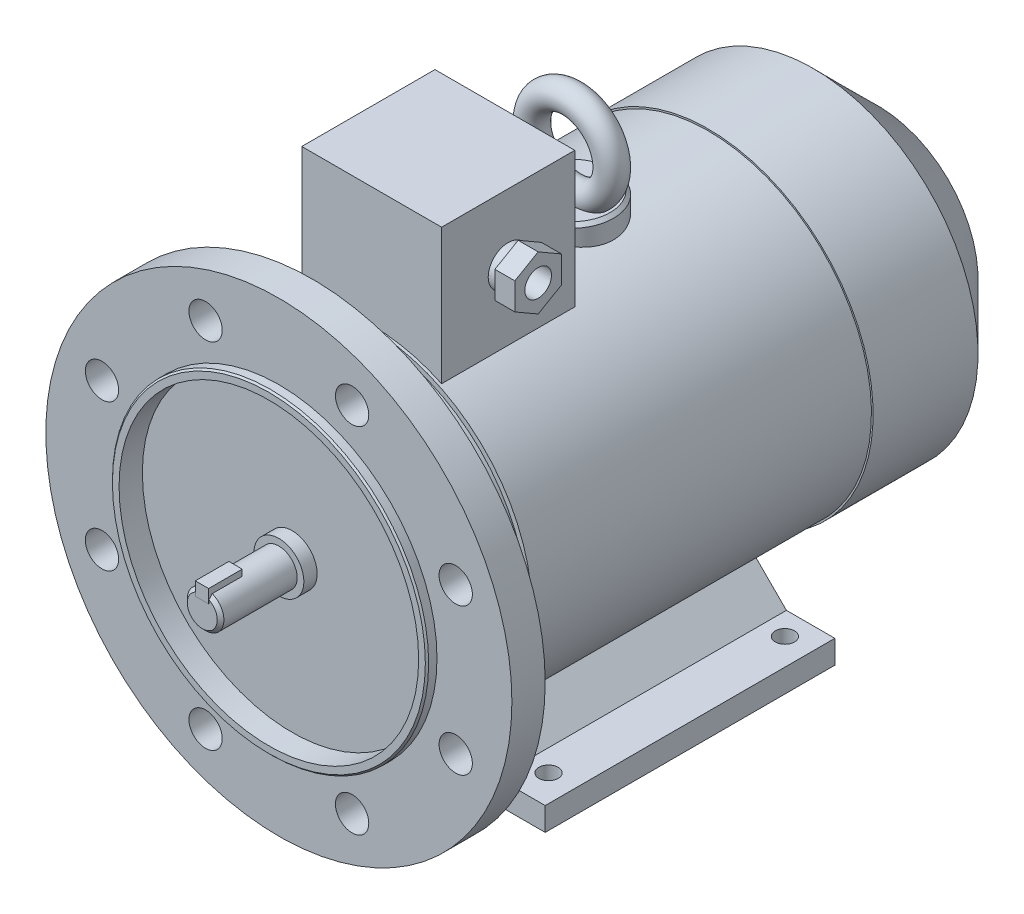
SolidWorks part; units mm, degrees
material "Ст.3 ГОСТ 380-88"
ref_plane "Спереди" through (0, 0, 0) normal (0, 0, 1) x (1, 0, 0)
ref_plane "Сверху" through (0, 0, 0) normal (0, 1, 0) x (1, 0, 0)
ref_plane "Справа" through (0, 0, 0) normal (1, 0, 0) x (0, 0, -1)
sketch "Эскиз1" plane through (0, 0, 0) normal (0, 0, 1) x (1, 0, 0)
  circle A0 centre (0, 0) radius 5.5
  dimension "D1" = 11
extrude "Вытянуть1" add sketch "Эскиз1" along normal blind 23
sketch "Эскиз2" plane through (0, 0, 23) normal (0, 0, 1) x (1, 0, 0)
  line L0 (0, 0) -> (0, 7.7807) construction
  line L1 (-2, 7) -> (2, 7)
  line L2 (-2, 7) -> (-2, 3)
  line L3 (-2, 3) -> (2, 3)
  line L4 (2, 7) -> (2, 3)
  circle A3 centre (0, 0) radius 5.5 construction
  dimension "D1" = 4
  dimension "D2" = 4
  dimension "D3" = 1.5
extrude "Вытянуть2" add sketch "Эскиз2" against normal blind 10 and the other way blind 0.1
sketch "Эскиз3" plane through (0, 0, 0) normal (0, 0, -1) x (-1, 0, 0)
  circle A0 centre (0, 0) radius 7.5
  dimension "D1" = 15
extrude "Вытянуть11" add sketch "Эскиз3" along normal blind 4
sketch "Эскиз16" plane through (0, 0, 0) normal (0, 0, 1) x (1, 0, 0)
  circle A0 centre (0, 0) radius 47.5
  circle A1 centre (0, 0) radius 70
  dimension "D1" = 95
  dimension "D2" = 140
extrude "Вытянуть13" add sketch "Эскиз16" against normal blind 10
sketch "Эскиз17" plane through (0, 0, -4) normal (0, 0, -1) x (-1, 0, 0)
  circle A0 centre (0, 0) radius 47.5
  dimension "D1" = 95
extrude "Вытянуть14" add sketch "Эскиз17" along normal blind 23
sketch "Эскиз18" plane through (0, 0, 0) normal (0, 0, 1) x (1, 0, 0)
  line L0 (0, 0) -> (0, 77.9559) construction
  line L1 (0, 0) -> (-29.3555, 70.8705) construction
  circle A0 centre (-22.0043, 53.1231) radius 5
  circle A3 centre (22.0043, 53.1231) radius 5
  circle A4 centre (53.1231, 22.0043) radius 5
  circle A5 centre (53.1231, -22.0043) radius 5
  circle A6 centre (22.0043, -53.1231) radius 5
  circle A7 centre (-22.0043, -53.1231) radius 5
  circle A8 centre (-53.1231, -22.0043) radius 5
  circle A9 centre (-53.1231, 22.0043) radius 5
  dimension "D2" = 10
  dimension "D1" = 22.5
  dimension "D3" = 57.5
  dimension "D4" = 57.5
  dimension "D5" = 57.5
extrude "Вырез-Вытянуть4" cut sketch "Эскиз18" against normal through all
sketch "Эскиз20" plane through (0, 0, -27) normal (0, 0, -1) x (-1, 0, 0)
  circle A0 centre (0, 0) radius 49
  dimension "D1" = 98
extrude "Вытянуть15" add sketch "Эскиз20" along normal blind 102
sketch "Эскиз21" plane through (0, 0, -129) normal (0, 0, -1) x (-1, 0, 0)
  circle A0 centre (0, 0) radius 49.5
  dimension "D1" = 99
extrude "Вытянуть16" add sketch "Эскиз21" along normal blind 51
chamfer "Фаска3" distance 19.5 angle 45 1 edges at (-49.5, 0, -180)
sketch "Эскиз22" plane through (0, 0, -27) normal (0, 0, 1) x (1, 0, 0)
  line L0 (-53, -56) -> (-32.6463, -56)
  line L1 (-32.6463, -56) -> (-14.1724, -37.5262)
  line L2 (-53, -56) -> (-53, -49)
  line L3 (-42, -56) -> (-44.9041, -56)
  line L4 (-53, -49) -> (-35.5458, -49)
  line L5 (-19.297, -32.7512) -> (-14.1724, -37.5262)
  line L6 (33.8559, -56) -> (53, -56)
  line L7 (-35.5458, -49) -> (-19.297, -32.7512)
  line L8 (42, -56) -> (43.6391, -56)
  line L9 (53, -56) -> (53, -49)
  line L10 (53, -49) -> (38.4542, -49)
  line L11 (33.8559, -56) -> (15.2435, -37.3877)
  line L12 (0, 0) -> (0, -80.1176) construction
  line L13 (38.4542, -49) -> (25.0733, -35.619)
  line L14 (25.0733, -35.619) -> (15.2435, -37.3877)
  circle A0 centre (0, 0) radius 70 construction
  circle M1 centre (0, 0) radius 49
  circle M2 centre (0, 0) radius 47.5
  dimension "D1" = 56
  dimension "D2" = 45
  dimension "D3" = 45
  dimension "D4" = 7
  dimension "D5" = 8.2013
  dimension "D6" = 7
  dimension "D7" = 7
  dimension "D8" = 106
  dimension "D9" = 53
  dimension "D10" = 74
  dimension "D11" = 66.5022
  dimension "D12" = 32.7512
  dimension "D13" = 35.619
  dimension "D14" = 37.5262
  dimension "D15" = 37.3877
extrude "Вытянуть17" add sketch "Эскиз22" against normal blind 87 contours L7 L4 L2 L0 L1 M1 | L7 L1 M1 M2 | L7 L1 L5 M2 | L10 L13 L11 L6 L9 M1 | L13 L14 L11 M2
sketch "Эскиз23" plane through (0, -56, 0) normal (0, -1, 0) x (1, 0, 0)
  line L0 (77.3931, -36) -> (-61.3551, -36) construction
  line L1 (77.3931, -107) -> (-64.6709, -107) construction
  line L2 (5.5, 23) -> (-5.5, 23) construction
  line L4 (45, -36) -> (-45, -36) construction
  line L5 (45, -36) -> (45, -107) construction
  circle A0 centre (45, -36) radius 2.9
  circle A1 centre (-45, -36) radius 2.9
  circle A2 centre (45, -107) radius 2.9
  circle A3 centre (-45, -107) radius 2.9
  dimension "D3" = 5.8
  dimension "D6" = 71
  dimension "D7" = 90
  dimension "D8" = 5.8
  dimension "D9" = 5.8
  dimension "D1" = 59
  dimension "D2" = 71
  dimension "D4" = 45
  dimension "D5" = 90
  dimension "D10" = 59
extrude "Вырез-Вытянуть5" cut sketch "Эскиз23" against normal up to next
ref_plane "Плоскость1" through (0, 42, 0) normal (0, 1, 0) x (-1, 0, 0)
sketch "Эскиз24" plane through (0, 42, 0) normal (0, 1, 0) x (-1, 0, 0)
  line L0 (0, 0) -> (0, -195.5205) construction
  line L1 (-21, -27.8856) -> (21, -27.8856)
  line L2 (-21, -27.8856) -> (-21, -67.8856)
  line L3 (-21, -67.8856) -> (21, -67.8856)
  line L4 (21, -27.8856) -> (21, -67.8856)
  line L7 (49, -27) -> (-49, -27) construction
  dimension "D1" = 42
  dimension "D2" = 42
  dimension "D3" = 40
  dimension "D4" = 40.8856
extrude "Вытянуть18" add sketch "Эскиз24" along normal blind 43
sketch "Эскиз25" plane through (0, 42, 0) normal (0, 1, 0) x (-1, 0, 0)
  line L0 (0, 0) -> (0, -180) construction
  line L1 (-30, -180) -> (30, -180) construction
  circle A0 centre (0, -88) radius 12.5
  dimension "D1" = 25
  dimension "D2" = 88
extrude "Вытянуть19" add sketch "Эскиз25" along normal blind 12
chamfer "Фаска4" distance 1 angle 45 1 edges at (0, 54, -75.5)
ref_plane "Плоскость2" through (0, 0, -88) normal (0, 0, 1) x (1, 0, 0)
sketch "Эскиз26" plane through (0, 0, -88) normal (0, 0, 1) x (1, 0, 0)
  line L0 (11.5, 54) -> (-11.5, 54) construction
  line L1 (0, 0) -> (0, 106.2294) construction
  circle A0 centre (0, 66) radius 12
  dimension "D1" = 24
sketch "Эскиз27" plane through (0, 0, 0) normal (1, 0, 0) x (0, 0, -1)
  line L0 (88, 0) -> (88, 106.2294) construction
  line L1 (99.5, 54) -> (76.5, 54) construction
  line L2 (88, 77) -> (88, -77) construction
  circle A0 centre (88, 78) radius 4
  dimension "D1" = 24
  dimension "D2" = 8
sweep "По траектории1" add profiles "Эскиз27" path "Эскиз26"
chamfer "Фаска5" distance 1 angle 45 1 edges at (0, -5.5, 23)
sketch "Эскиз28" plane through (0, 0, -4) normal (0, 0, 1) x (1, 0, 0)
  circle A0 centre (0, 0) radius 47.5
  circle A1 centre (0, 0) radius 45
  dimension "D1" = 90
  dimension "D2" = 95
extrude "Вытянуть20" add sketch "Эскиз28" along normal blind 7
chamfer "Фаска6" distance 0.5 angle 45 1 edges at (47.5, 0, 3)
sketch "Эскиз29" plane through (21, 0, 0) normal (1, 0, 0) x (0, 0, -1)
  line L0 (27.8856, 85) -> (67.8856, 85) construction
  line L1 (27.8856, 85) -> (27.8856, 44.2719) construction
  circle A0 centre (47.8856, 65) radius 6
  dimension "D3" = 12
  dimension "D1" = 20
  dimension "D2" = 20
extrude "Вытянуть21" add sketch "Эскиз29" along normal blind 3
sketch "Эскиз30" plane through (24, 0, 0) normal (1, 0, 0) x (0, 0, -1)
  line L0 (47.8856, 65) -> (47.8856, 88.5651) construction
  line L1 (47.8856, 73.0829) -> (40.8856, 69.0415)
  line L2 (40.8856, 69.0415) -> (40.8856, 60.9585)
  line L3 (40.8856, 60.9585) -> (47.8856, 56.9171)
  line L4 (47.8856, 56.9171) -> (54.8856, 60.9585)
  line L5 (54.8856, 60.9585) -> (54.8856, 69.0415)
  line L6 (54.8856, 69.0415) -> (47.8856, 73.0829)
  circle A0 centre (47.8856, 65) radius 7 construction
  circle A1 centre (47.8856, 65) radius 6 construction
  dimension "D1" = 14
extrude "Вытянуть22" add sketch "Эскиз30" along normal blind 6
sketch "Эскиз31" plane through (30, 0, 0) normal (1, 0, 0) x (0, 0, -1)
  line L0 (27.8856, 85) -> (67.8856, 85) construction
  line L1 (27.8856, 85) -> (27.8856, 44.2719) construction
  circle A0 centre (47.8856, 65) radius 4
  dimension "D1" = 8
  dimension "D2" = 20
  dimension "D3" = 20
extrude "Вырез-Вытянуть6" cut sketch "Эскиз31" against normal blind 10
